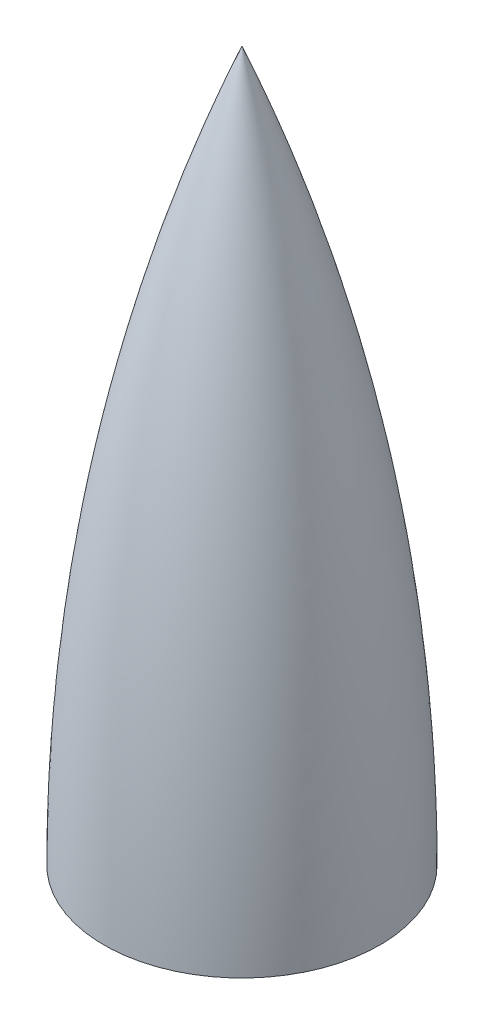
SolidWorks part; units mm, degrees
ref_plane "Front Plane" through (0, 0, 0) normal (0, 0, 1) x (1, 0, 0)
ref_plane "Top Plane" through (0, 0, 0) normal (0, 1, 0) x (1, 0, 0)
ref_plane "Right Plane" through (0, 0, 0) normal (1, 0, 0) x (0, 0, -1)
sketch "Sketch1" plane through (0, 0, 0) normal (0, 0, 1) x (1, 0, 0)
  line L2 (0, 0) -> (3500, 0)
  line L3 (0, 0) -> (0, 18000)
  arc A2 (3500, 0) -> (0, 18000) centre (-44535, 0.1389) ccw
  point P9 (660.5561, 18000)
  point P10 (4223.8048, 0)
  dimension "D1" = 3500
  dimension "D3" = 18000
revolve "Revolve2" add sketch "Sketch1" angle 360 about L3
